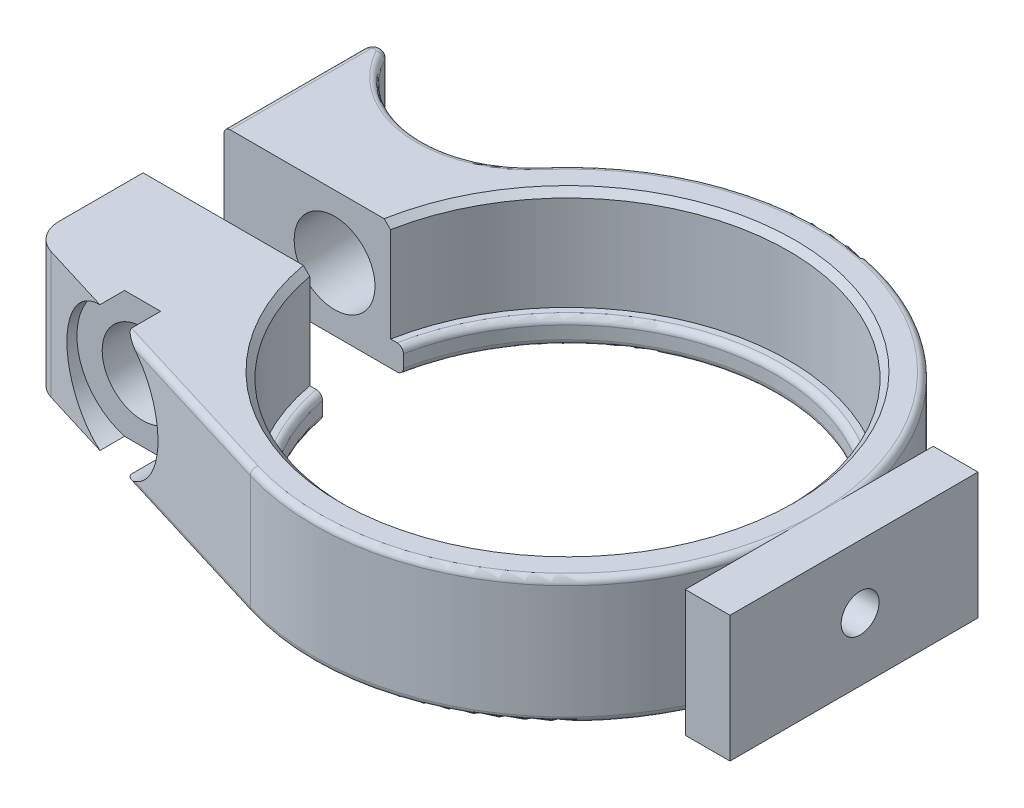
SolidWorks part; units mm, degrees
material "В95Т ГОСТ 4784-97"
ref_plane "Спереди" through (0, 0, 0) normal (0, 0, 1) x (1, 0, 0)
ref_plane "Сверху" through (0, 0, 0) normal (0, 1, 0) x (1, 0, 0)
ref_plane "Справа" through (0, 0, 0) normal (1, 0, 0) x (0, 0, -1)
sketch "Масса" [suppressed] plane through (0, 0, 0) normal (0, 0, 1) x (1, 0, 0)
  point P0 (0, 20.71)
  dimension "D1" = 20.71
sketch "Эскиз1" plane through (0, 0, 0) normal (0, 1, 0) x (1, 0, 0)
  line L0 (0, 0) -> (-30.4, 0) construction
  line L1 (-30.4, 28.5784) -> (-30.4, -28.5784) construction
  line L2 (-5.894, -19.2164) -> (-28.6331, -12.2419)
  line L3 (-30.4, 3.2) -> (-16.1867, 3.2)
  line L4 (-30.4, -3.2) -> (-16.1867, -3.2)
  line L5 (-16.1867, 3.2) -> (-16.1867, -3.2) construction
  line L6 (-29.7, 14.965) -> (-36.5107, 14.965) construction
  line L7 (-21.6395, 10.2) -> (-30.4, 10.2) construction
  line L8 (20.1, 0) -> (20.1, -17.9644) construction
  line L9 (-30.4, 3.2) -> (-30.4, 14.265)
  line L10 (-30.4, 14.265) -> (-30.4343, 14.2465)
  line L11 (-30.4, -9.8518) -> (-30.4, -3.2)
  line L13 (25.1, -5.1845) -> (20.1, -5.1845)
  line L14 (25.1, -5.1845) -> (25.1, 10.8155)
  line L15 (25.1, 10.8155) -> (20.1, 10.8155)
  line L16 (20.1, -5.1845) -> (20.1, 10.8155)
  circle A0 centre (0, 0) radius 16.5 construction
  arc A1 (-16.1867, 3.2) -> (-16.1867, -3.2) centre (0, 0) cw
  arc A2 (-5.894, -19.2164) -> (-15.2082, 13.1423) centre (0, 0) ccw
  arc A3 (-15.2082, 13.1423) -> (-29.0867, 14.6025) centre (-21.6395, 18.7) cw
  arc A4 (-29.0867, 14.6025) -> (-30.4, 14.265) centre (-29.7, 14.265) ccw
  arc A5 (-28.6331, -12.2419) -> (-30.4, -9.8518) centre (-27.9, -9.8518) cw
  point P5 (-30.4, 0)
  point P27 (-30.4, -11.7)
  dimension "D1" = 33
  dimension "D4" = 20.1
  dimension "D5" = 0.7
  dimension "D7" = 8.5
  dimension "D10" = 2.5
  dimension "D11" = 5
  dimension "D2" = 8.5
  dimension "D3" = 6.4
  dimension "D6" = 11.765
  dimension "D8" = 7
  dimension "D9" = 50.5
  dimension "D12" = 5
  dimension "D13" = 16
extrude "Бобышка-Вытянуть1" add sketch "Эскиз1" along normal mid plane 10 contours A5 L2 A2 A3 A4 L9 L3 A1 L4 L11
sketch "Эскиз2" plane through (0, 5, 0) normal (0, 1, 0) x (1, 0, 0)
  circle A0 centre (0, 0) radius 17.5
  dimension "D1" = 35
extrude "Вырез-Вытянуть1" cut sketch "Эскиз2" against normal offset from surface (8 mm away) 2 up to face at (-17.1148, -5, -0.5889)
sketch "Эскиз4" plane through (0, 0, 0) normal (0, 1, 0) x (1, 0, 0)
  line L0 (-21.6395, 18.7) -> (-21.6395, -48.7253) construction
  line L1 (0, 0) -> (-21.6395, 0) construction
  line L2 (-24.8395, 16.7848) -> (-24.8395, -12)
  line L3 (-24.8395, -12) -> (-26.8395, -12)
  line L4 (-26.8395, -12) -> (-26.8395, -19.6337)
  line L5 (-26.8395, -19.6337) -> (-21.6395, -19.6337)
  line L6 (-21.6395, -19.6337) -> (-21.6395, 16.7848)
  line L7 (-24.8395, 16.7848) -> (-21.6395, 16.7848)
  dimension "D1" = 10.4
  dimension "D2" = 6.4
  dimension "D3" = 12
revolve "Вырез-Повернуть1" cut sketch "Эскиз4" angle 360 about L0
chamfer "Фаска1" distance 0.5 angle 45 1 edges at (17.5, 5, 0)
sketch "Sketch4" plane through (0, -5, 0) normal (0, -1, 0) x (1, 0, 0)
  line L1 (23.1677, 10.3028) -> (19.6288, 10.3028)
  line L2 (23.1677, 10.3028) -> (23.1677, -9.3324)
  line L3 (23.1677, -9.3324) -> (19.6288, -9.3324)
  line L4 (19.6288, 10.3028) -> (19.6288, -9.3324)
extrude "Boss-Extrude1" add sketch "Sketch4" against normal blind 10 separate body
fillet "Скругление1" radius 0.5 12 edges at (-13.0526, -5, 17.0207) (-22.5289, -5, -10.2467) (-13.0526, 5, 17.0207) (-22.5289, 5, -10.2467) (16.5, -3, 0) (16.5, -5, 0) (19.3157, -5, -5.5599) (19.3157, 5, -5.5599) (-30.4, -5, -8.7325) (-29.8742, -5, -14.943) (-30.4, 5, -8.7325) (-29.8742, 5, -14.943)
sketch "Sketch5" plane through (23.1677, 0, 0) normal (1, 0, 0) x (0, 0, -1)
  circle A0 centre (0, 0) radius 1.5
extrude "Cut-Extrude1" cut sketch "Sketch5" against normal blind 10
equation "\"D1@Масса\"=\"SW-Масса\""
